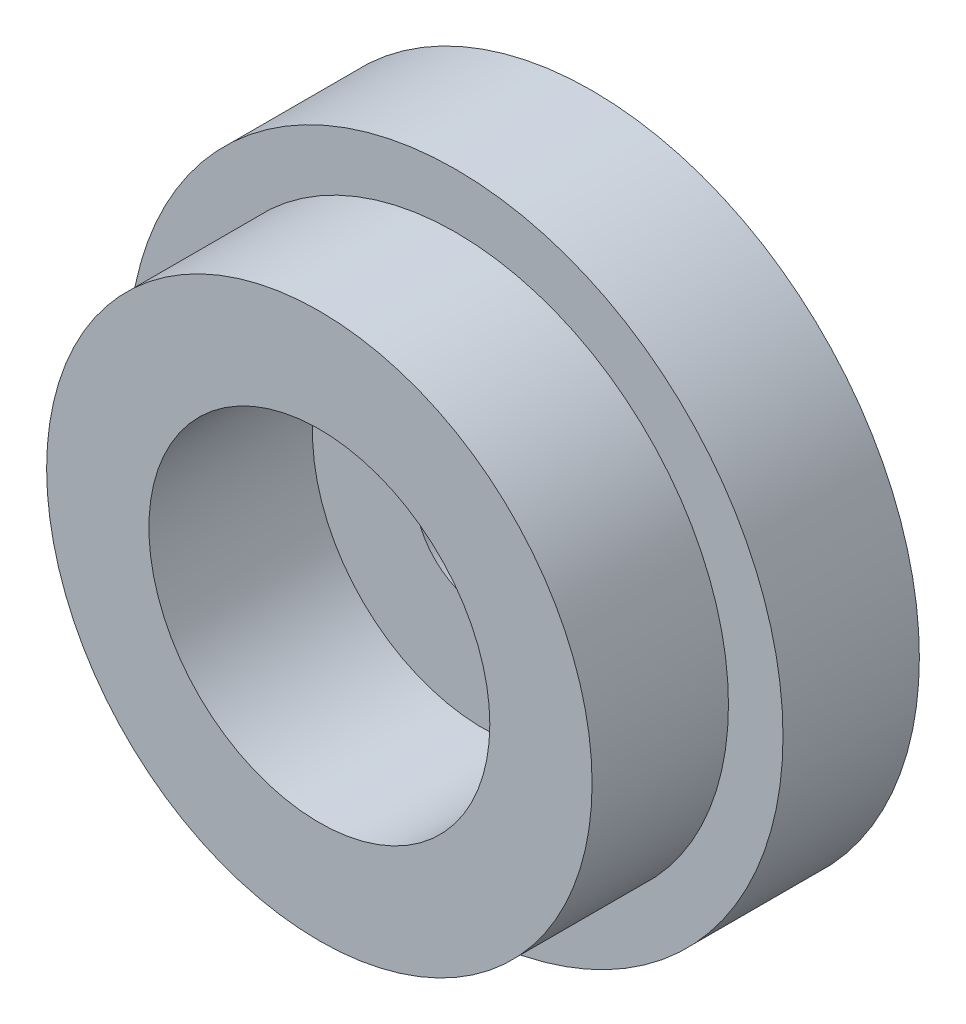
SolidWorks part; units mm, degrees
ref_plane "前视基准面" through (0, 0, 0) normal (0, 0, 1) x (1, 0, 0)
ref_plane "上视基准面" through (0, 0, 0) normal (0, 1, 0) x (1, 0, 0)
ref_plane "右视基准面" through (0, 0, 0) normal (1, 0, 0) x (0, 0, -1)
sketch "草图1" plane through (0, 0, 0) normal (1, 0, 0) x (0, 0, -1)
  line L0 (0, 0) -> (45.9486, 0) construction
  line L1 (0, 0) -> (0, 24)
  line L2 (0, 24) -> (10, 24)
  line L3 (10, 24) -> (10, 10.45)
  line L4 (10, 10.45) -> (8, 10.45)
  line L5 (8, 10.45) -> (8, 0)
  line L6 (8, 0) -> (0, 0)
  dimension "D1" = 2
  dimension "D2" = 20.9
  dimension "D3" = 48
  dimension "D4" = 10
revolve "旋转1" add sketch "草图1" angle 360 about L0
sketch "草图2" plane through (0, 0, 0) normal (0, 0, 1) x (1, 0, 0)
  circle A0 centre (0, 0) radius 20
  dimension "D1" = 40
extrude "凸台-拉伸1" add sketch "草图2" along normal blind 10
sketch "草图3" plane through (0, 0, 10) normal (0, 0, 1) x (1, 0, 0)
  circle A0 centre (0, 0) radius 5
  dimension "D1" = 10
extrude "切除-拉伸1" cut sketch "草图3" against normal through all
sketch "草图4" plane through (0, 0, 10) normal (0, 0, 1) x (1, 0, 0)
  circle A0 centre (0, 0) radius 12.5
  dimension "D1" = 25
extrude "切除-拉伸2" cut sketch "草图4" against normal blind 12
